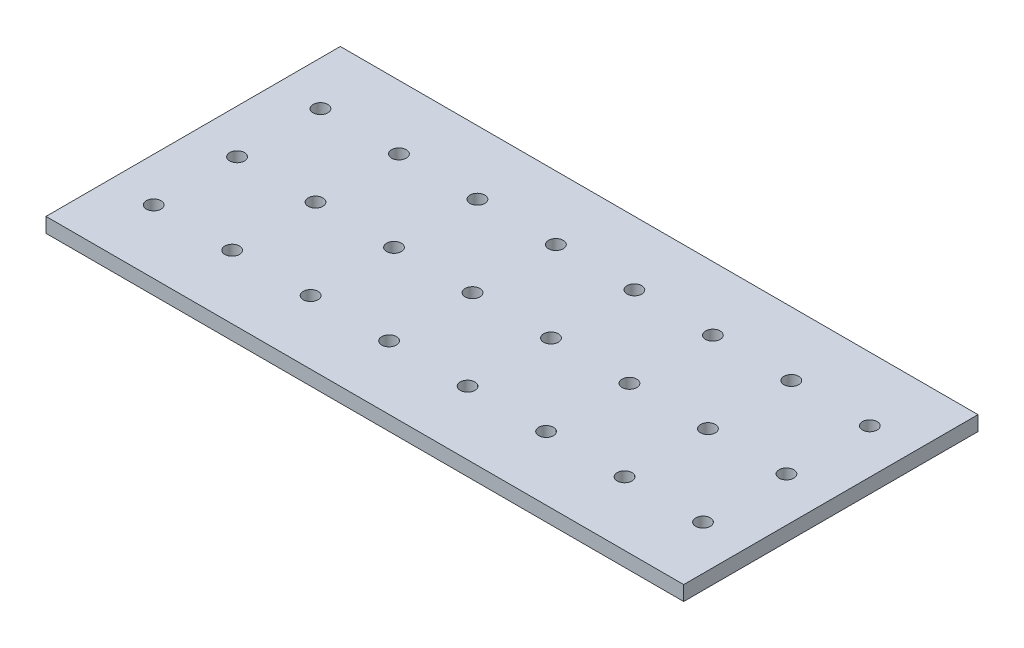
SolidWorks part; units mm, degrees
ref_plane "Спереди" through (0, 0, 0) normal (0, 0, 1) x (1, 0, 0)
ref_plane "Сверху" through (0, 0, 0) normal (0, 1, 0) x (1, 0, 0)
ref_plane "Справа" through (0, 0, 0) normal (1, 0, 0) x (0, 0, -1)
other "Configuration Table"
sketch "Эскиз1" plane through (0, 0, 0) normal (0, 1, 0) x (1, 0, 0)
  line L1 (-65, 30) -> (65, 30)
  line L2 (-65, 30) -> (-65, -30)
  line L3 (-65, -30) -> (65, -30)
  line L4 (65, 30) -> (65, -30)
  line L5 (0, -30) -> (0, 30) construction
  line L6 (-65, 0) -> (65, 0) construction
  point P0 (0, 0)
  dimension "D1" = 130
  dimension "D2" = 60
extrude "Бобышка-Вытянуть1" add sketch "Эскиз1" along normal blind 3
sketch "Эскиз2" plane through (0, 3, 0) normal (0, 1, 0) x (1, 0, 0)
  line L0 (-65, 17) -> (65, 17) construction
  line L1 (-65, 30) -> (-65, -30) construction
  line L2 (65, -30) -> (65, 30) construction
  line L3 (-65, -17) -> (65, -17) construction
  line L4 (-65, 0) -> (65, 0) construction
  line L5 (65, 30) -> (-65, 30) construction
  line L6 (-65, -30) -> (65, -30) construction
  line L7 (0, 30) -> (0, -30) construction
  line L8 (-56.0527, 30) -> (-56.0527, -30) construction
  line L9 (-49, -17) -> (81, -17) construction
  line L10 (-49, 0) -> (81, 0) construction
  line L11 (-40.0527, 30) -> (-40.0527, -30) construction
  line L12 (-33, -17) -> (97, -17) construction
  line L13 (-33, 0) -> (97, 0) construction
  line L14 (-24.0527, 30) -> (-24.0527, -30) construction
  line L15 (-17, -17) -> (113, -17) construction
  line L16 (-17, 0) -> (113, 0) construction
  line L17 (-8.0527, 30) -> (-8.0527, -30) construction
  line L18 (-1, -17) -> (129, -17) construction
  line L19 (-1, 0) -> (129, 0) construction
  line L20 (7.9473, 30) -> (7.9473, -30) construction
  line L21 (15, -17) -> (145, -17) construction
  line L22 (15, 0) -> (145, 0) construction
  line L23 (23.9473, 30) -> (23.9473, -30) construction
  line L24 (31, -17) -> (161, -17) construction
  line L25 (31, 0) -> (161, 0) construction
  line L26 (39.9473, 30) -> (39.9473, -30) construction
  line L27 (47, -17) -> (177, -17) construction
  line L28 (47, 0) -> (177, 0) construction
  line L29 (55.9473, 30) -> (55.9473, -30) construction
  circle A0 centre (-56.0527, 17) radius 1.5
  circle A1 centre (-40.0527, 17) radius 1.5
  circle A2 centre (-24.0527, 17) radius 1.5
  circle A3 centre (-8.0527, 17) radius 1.5
  circle A4 centre (7.9473, 17) radius 1.5
  circle A5 centre (23.9473, 17) radius 1.5
  circle A6 centre (39.9473, 17) radius 1.5
  circle A7 centre (55.9473, 17) radius 1.5
  circle A8 centre (-56.0527, 0) radius 1.5
  circle A9 centre (-56.0527, -17) radius 1.5
  circle A10 centre (-40.0527, 0) radius 1.5
  circle A11 centre (-40.0527, -17) radius 1.5
  circle A12 centre (-24.0527, 0) radius 1.5
  circle A13 centre (-24.0527, -17) radius 1.5
  circle A14 centre (-8.0527, 0) radius 1.5
  circle A15 centre (-8.0527, -17) radius 1.5
  circle A16 centre (7.9473, 0) radius 1.5
  circle A17 centre (7.9473, -17) radius 1.5
  circle A18 centre (23.9473, 0) radius 1.5
  circle A19 centre (23.9473, -17) radius 1.5
  circle A20 centre (39.9473, 0) radius 1.5
  circle A21 centre (39.9473, -17) radius 1.5
  circle A22 centre (55.9473, 0) radius 1.5
  circle A23 centre (55.9473, -17) radius 1.5
  dimension "D3" = 8
  dimension "D4" = 8
  dimension "D1" = 13
  dimension "D2" = 13
extrude "Вырез-Вытянуть1" cut sketch "Эскиз2" against normal blind 3
